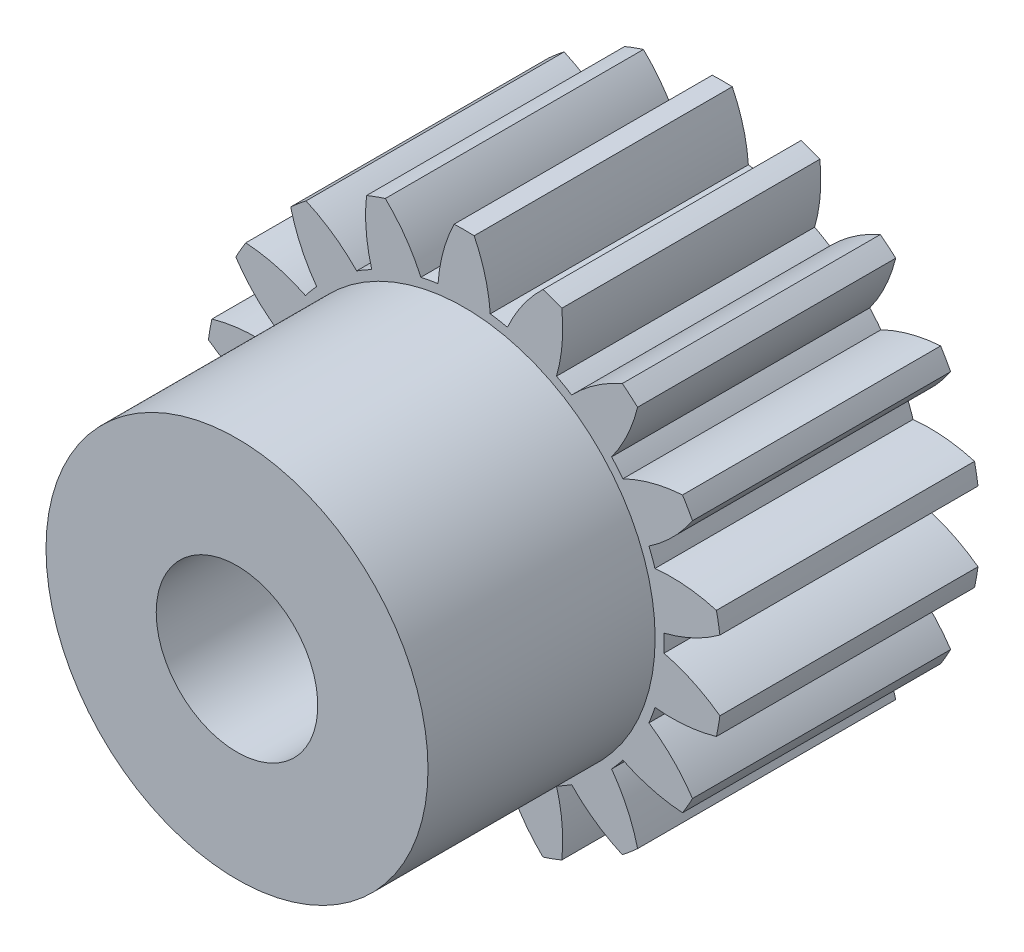
SolidWorks part; units mm, degrees
ref_plane "Front Plane" through (0, 0, 0) normal (0, 0, 1) x (1, 0, 0)
ref_plane "Top Plane" through (0, 0, 0) normal (0, 1, 0) x (1, 0, 0)
ref_plane "Right Plane" through (0, 0, 0) normal (1, 0, 0) x (0, 0, -1)
sketch "Sketch1" plane through (0, 0, 0) normal (0, 1, 0) x (1, 0, 0)
  line L0 (12.7, 12.7) -> (0, 12.7)
  line L1 (0, 12.7) -> (0, 0)
  line L2 (0, 0) -> (12.7, 0)
  line L3 (12.7, 0) -> (12.7, 12.7)
  line L4 (0, 12.7) -> (0, 0) construction
revolve "Revolve1" add sketch "Sketch1" angle 360 about L4
sketch "Sketch2" plane through (0, 0, -12.7) normal (0, 0, -1) x (-1, 0, 0)
  arc A0 (8.5344, 9.405) -> (7.2566, 6.6496) centre (0.8613, 11.2895) cw
  arc A1 (7.2566, 6.6496) -> (7.8086, 5.9916) centre (0, 0) cw
  arc A2 (7.8086, 5.9916) -> (10.7441, 6.7716) centre (11.2675, -1.1122) cw
  arc A3 (10.7441, 6.7716) -> (8.5344, 9.405) centre (0, 0) ccw
extrude "Cut-Extrude1" cut sketch "Sketch2" against normal through all
sketch "Sketch3" plane through (0, 0, -12.7) normal (0, 0, -1) x (-1, 0, 0)
  arc A0 (11.2364, 5.9188) -> (9.0932, 3.7667) centre (4.6706, 10.314) cw
  arc A1 (9.0932, 3.7667) -> (9.387, 2.9596) centre (0, 0) cw
  arc A2 (9.387, 2.9596) -> (12.4121, 2.6885) centre (10.2076, -4.8988) cw
  arc A3 (12.4121, 2.6885) -> (11.2364, 5.9188) centre (0, 0) ccw
extrude "Cut-Extrude2" cut sketch "Sketch3" against normal through all
sketch "Sketch4" plane through (0, 0, -12.7) normal (0, 0, -1) x (-1, 0, 0)
  arc A0 (12.5831, 1.7188) -> (9.8331, 0.4294) centre (7.9165, 8.0946) cw
  arc A1 (9.8331, 0.4294) -> (9.8331, -0.4294) centre (0, 0) cw
  arc A2 (9.8331, -0.4294) -> (12.5831, -1.7188) centre (7.9165, -8.0946) cw
  arc A3 (12.5831, -1.7188) -> (12.5831, 1.7188) centre (0, 0) ccw
extrude "Cut-Extrude3" cut sketch "Sketch4" against normal through all
sketch "Sketch5" plane through (0, 0, -12.7) normal (0, 0, -1) x (-1, 0, 0)
  arc A0 (12.4121, -2.6885) -> (9.387, -2.9596) centre (10.2076, 4.8988) cw
  arc A1 (9.387, -2.9596) -> (9.0932, -3.7667) centre (0, 0) cw
  arc A2 (9.0932, -3.7667) -> (11.2364, -5.9188) centre (4.6706, -10.314) cw
  arc A3 (11.2364, -5.9188) -> (12.4121, -2.6885) centre (0, 0) ccw
extrude "Cut-Extrude4" cut sketch "Sketch5" against normal through all
sketch "Sketch6" plane through (0, 0, -12.7) normal (0, 0, -1) x (-1, 0, 0)
  arc A0 (10.7441, -6.7716) -> (7.8086, -5.9916) centre (11.2675, 1.1122) cw
  arc A1 (7.8086, -5.9916) -> (7.2566, -6.6496) centre (0, 0) cw
  arc A2 (7.2566, -6.6496) -> (8.5344, -9.405) centre (0.8613, -11.2895) cw
  arc A3 (8.5344, -9.405) -> (10.7441, -6.7716) centre (0, 0) ccw
extrude "Cut-Extrude5" cut sketch "Sketch6" against normal through all
sketch "Sketch7" plane through (0, 0, -12.7) normal (0, 0, -1) x (-1, 0, 0)
  arc A0 (7.7801, -10.0379) -> (5.2885, -8.301) centre (10.9684, -2.8086) cw
  arc A1 (5.2885, -8.301) -> (4.5447, -8.7304) centre (0, 0) cw
  arc A2 (4.5447, -8.7304) -> (4.803, -11.7567) centre (-3.0519, -10.9032) cw
  arc A3 (4.803, -11.7567) -> (7.7801, -10.0379) centre (0, 0) ccw
extrude "Cut-Extrude6" cut sketch "Sketch7" against normal through all
sketch "Sketch8" plane through (0, 0, -12.7) normal (0, 0, -1) x (-1, 0, 0)
  arc A0 (3.8777, -12.0935) -> (2.1304, -9.6092) centre (9.3463, -6.3906) cw
  arc A1 (2.1304, -9.6092) -> (1.2846, -9.7583) centre (0, 0) cw
  arc A2 (1.2846, -9.7583) -> (0.4924, -12.6904) centre (-6.5969, -9.2019) cw
  arc A3 (0.4924, -12.6904) -> (3.8777, -12.0935) centre (0, 0) ccw
extrude "Cut-Extrude7" cut sketch "Sketch8" against normal through all
sketch "Sketch9" plane through (0, 0, -12.7) normal (0, 0, -1) x (-1, 0, 0)
  arc A0 (-0.4924, -12.6904) -> (-1.2846, -9.7583) centre (6.5969, -9.2019) cw
  arc A1 (-1.2846, -9.7583) -> (-2.1304, -9.6092) centre (0, 0) cw
  arc A2 (-2.1304, -9.6092) -> (-3.8777, -12.0935) centre (-9.3463, -6.3906) cw
  arc A3 (-3.8777, -12.0935) -> (-0.4924, -12.6904) centre (0, 0) ccw
extrude "Cut-Extrude8" cut sketch "Sketch9" against normal through all
sketch "Sketch10" plane through (0, 0, -12.7) normal (0, 0, -1) x (-1, 0, 0)
  arc A0 (-4.803, -11.7567) -> (-4.5447, -8.7304) centre (3.0519, -10.9032) cw
  arc A1 (-4.5447, -8.7304) -> (-5.2885, -8.301) centre (0, 0) cw
  arc A2 (-5.2885, -8.301) -> (-7.7801, -10.0379) centre (-10.9684, -2.8086) cw
  arc A3 (-7.7801, -10.0379) -> (-4.803, -11.7567) centre (0, 0) ccw
extrude "Cut-Extrude9" cut sketch "Sketch10" against normal through all
sketch "Sketch11" plane through (0, 0, -12.7) normal (0, 0, -1) x (-1, 0, 0)
  arc A0 (-8.5344, -9.405) -> (-7.2566, -6.6496) centre (-0.8613, -11.2895) cw
  arc A1 (-7.2566, -6.6496) -> (-7.8086, -5.9916) centre (0, 0) cw
  arc A2 (-7.8086, -5.9916) -> (-10.7441, -6.7716) centre (-11.2675, 1.1122) cw
  arc A3 (-10.7441, -6.7716) -> (-8.5344, -9.405) centre (0, 0) ccw
extrude "Cut-Extrude10" cut sketch "Sketch11" against normal through all
sketch "Sketch12" plane through (0, 0, -12.7) normal (0, 0, -1) x (-1, 0, 0)
  arc A0 (-11.2364, -5.9188) -> (-9.0932, -3.7667) centre (-4.6706, -10.314) cw
  arc A1 (-9.0932, -3.7667) -> (-9.387, -2.9596) centre (0, 0) cw
  arc A2 (-9.387, -2.9596) -> (-12.4121, -2.6885) centre (-10.2076, 4.8988) cw
  arc A3 (-12.4121, -2.6885) -> (-11.2364, -5.9188) centre (0, 0) ccw
extrude "Cut-Extrude11" cut sketch "Sketch12" against normal through all
sketch "Sketch13" plane through (0, 0, -12.7) normal (0, 0, -1) x (-1, 0, 0)
  arc A0 (-12.5831, -1.7188) -> (-9.8331, -0.4294) centre (-7.9165, -8.0946) cw
  arc A1 (-9.8331, -0.4294) -> (-9.8331, 0.4294) centre (0, 0) cw
  arc A2 (-9.8331, 0.4294) -> (-12.5831, 1.7188) centre (-7.9165, 8.0946) cw
  arc A3 (-12.5831, 1.7188) -> (-12.5831, -1.7188) centre (0, 0) ccw
extrude "Cut-Extrude12" cut sketch "Sketch13" against normal through all
sketch "Sketch14" plane through (0, 0, -12.7) normal (0, 0, -1) x (-1, 0, 0)
  arc A0 (-12.4121, 2.6885) -> (-9.387, 2.9596) centre (-10.2076, -4.8988) cw
  arc A1 (-9.387, 2.9596) -> (-9.0932, 3.7667) centre (0, 0) cw
  arc A2 (-9.0932, 3.7667) -> (-11.2364, 5.9188) centre (-4.6706, 10.314) cw
  arc A3 (-11.2364, 5.9188) -> (-12.4121, 2.6885) centre (0, 0) ccw
extrude "Cut-Extrude13" cut sketch "Sketch14" against normal through all
sketch "Sketch15" plane through (0, 0, -12.7) normal (0, 0, -1) x (-1, 0, 0)
  arc A0 (-10.7441, 6.7716) -> (-7.8086, 5.9916) centre (-11.2675, -1.1122) cw
  arc A1 (-7.8086, 5.9916) -> (-7.2566, 6.6496) centre (0, 0) cw
  arc A2 (-7.2566, 6.6496) -> (-8.5344, 9.405) centre (-0.8613, 11.2895) cw
  arc A3 (-8.5344, 9.405) -> (-10.7441, 6.7716) centre (0, 0) ccw
extrude "Cut-Extrude14" cut sketch "Sketch15" against normal through all
sketch "Sketch16" plane through (0, 0, -12.7) normal (0, 0, -1) x (-1, 0, 0)
  arc A0 (-7.7801, 10.0379) -> (-5.2885, 8.301) centre (-10.9684, 2.8086) cw
  arc A1 (-5.2885, 8.301) -> (-4.5447, 8.7304) centre (0, 0) cw
  arc A2 (-4.5447, 8.7304) -> (-4.803, 11.7567) centre (3.0519, 10.9032) cw
  arc A3 (-4.803, 11.7567) -> (-7.7801, 10.0379) centre (0, 0) ccw
extrude "Cut-Extrude15" cut sketch "Sketch16" against normal through all
sketch "Sketch17" plane through (0, 0, -12.7) normal (0, 0, -1) x (-1, 0, 0)
  arc A0 (-3.8777, 12.0935) -> (-2.1304, 9.6092) centre (-9.3463, 6.3906) cw
  arc A1 (-2.1304, 9.6092) -> (-1.2846, 9.7583) centre (0, 0) cw
  arc A2 (-1.2846, 9.7583) -> (-0.4924, 12.6904) centre (6.5969, 9.2019) cw
  arc A3 (-0.4924, 12.6904) -> (-3.8777, 12.0935) centre (0, 0) ccw
extrude "Cut-Extrude16" cut sketch "Sketch17" against normal through all
sketch "Sketch18" plane through (0, 0, -12.7) normal (0, 0, -1) x (-1, 0, 0)
  arc A0 (0.4924, 12.6904) -> (1.2846, 9.7583) centre (-6.5969, 9.2019) cw
  arc A1 (1.2846, 9.7583) -> (2.1304, 9.6092) centre (0, 0) cw
  arc A2 (2.1304, 9.6092) -> (3.8777, 12.0935) centre (9.3463, 6.3906) cw
  arc A3 (3.8777, 12.0935) -> (0.4924, 12.6904) centre (0, 0) ccw
extrude "Cut-Extrude17" cut sketch "Sketch18" against normal through all
sketch "Sketch19" plane through (0, 0, -12.7) normal (0, 0, -1) x (-1, 0, 0)
  arc A0 (4.803, 11.7567) -> (4.5447, 8.7304) centre (-3.0519, 10.9032) cw
  arc A1 (4.5447, 8.7304) -> (5.2885, 8.301) centre (0, 0) cw
  arc A2 (5.2885, 8.301) -> (7.7801, 10.0379) centre (10.9684, 2.8086) cw
  arc A3 (7.7801, 10.0379) -> (4.803, 11.7567) centre (0, 0) ccw
extrude "Cut-Extrude18" cut sketch "Sketch19" against normal through all
sketch "Sketch20" plane through (0, 0, 0) normal (0, 1, 0) x (1, 0, 0)
  line L0 (9.398, 0) -> (0, 0)
  line L1 (0, 0) -> (0, -11.176)
  line L2 (0, -11.176) -> (9.398, -11.176)
  line L3 (9.398, -11.176) -> (9.398, 0)
  line L4 (0, 0) -> (0, -11.176) construction
revolve "Revolve2" add sketch "Sketch20" angle 360 about L4
hole_wizard "Hole1" positions "Sketch22" profile "Sketch21" legacy
sketch "Sketch22" plane through (0, 0, -12.7) normal (0, 0, -1) x (-1, 0, 0)
  point P0 (0, 0)
sketch "Sketch21" plane through (0, 0, -12.7) normal (1, 0, 0) x (0, 1, 0)
  line L0 (0, 0) -> (0, 23.876)
  line L1 (0, 23.876) -> (3.9751, 23.876)
  line L2 (3.9751, 23.876) -> (3.9751, 0)
  line L3 (3.9751, 0) -> (0, 0)
  line L4 (0, 110) -> (0, -10) construction
  dimension "Diameter" = 7.9502
  dimension "Depth" = 23.876
